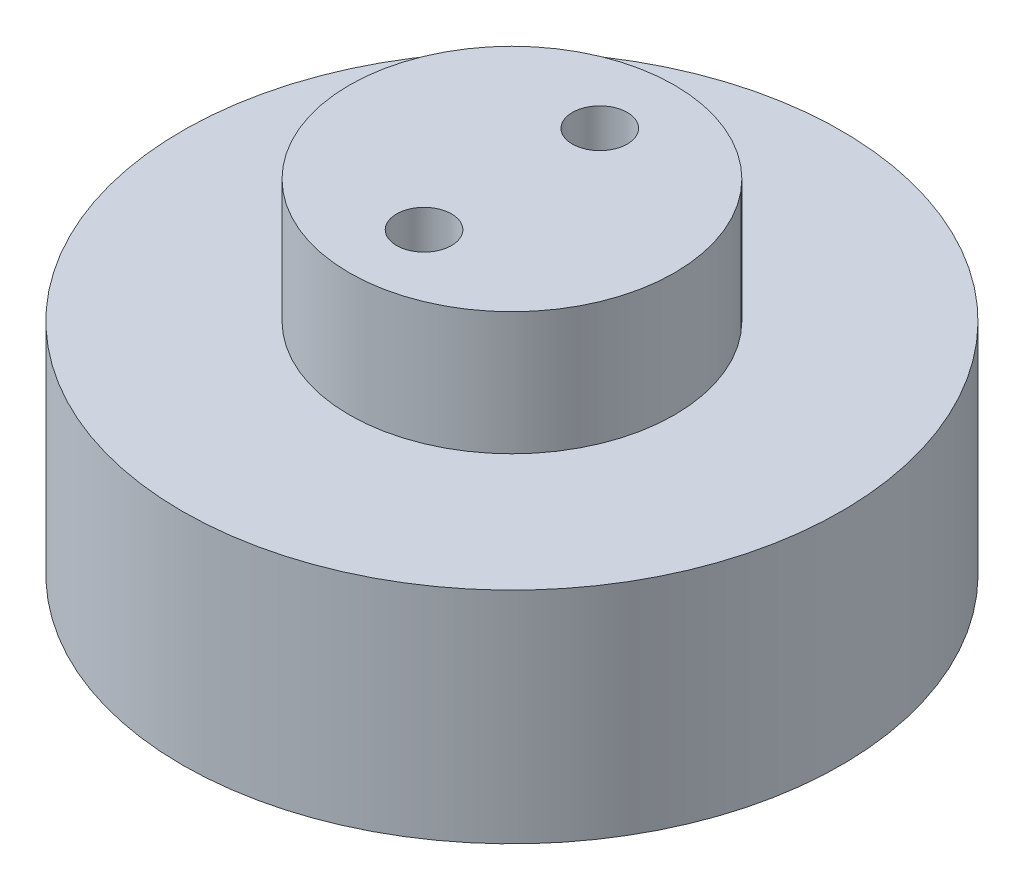
SolidWorks part; units mm, degrees
ref_plane "Front Plane" through (0, 0, 0) normal (0, 0, 1) x (1, 0, 0)
ref_plane "Top Plane" through (0, 0, 0) normal (0, 1, 0) x (1, 0, 0)
ref_plane "Right Plane" through (0, 0, 0) normal (1, 0, 0) x (0, 0, -1)
sketch "Sketch1" plane through (0, 0, 0) normal (0, 1, 0) x (1, 0, 0)
  circle A0 centre (0, 0) radius 19.05
  dimension "D1" = 38.1
extrude "Boss-Extrude1" add sketch "Sketch1" along normal blind 12.7
sketch "Sketch2" plane through (0, 12.7, 0) normal (0, 1, 0) x (1, 0, 0)
  circle A0 centre (0, 0) radius 9.398
  dimension "D1" = 18.796
extrude "Boss-Extrude2" add sketch "Sketch2" along normal blind 7.112
sketch "Sketch3" plane through (0, 0, 0) normal (0, -1, 0) x (1, 0, 0)
  circle A0 centre (0, 0) radius 2.921
  dimension "D1" = 5.842
extrude "Cut-Extrude1" [suppressed] cut sketch "Sketch3" against normal blind 17.272
sketch "Sketch4" [suppressed] plane through (0, 17.272, 0) normal (0, -1, 0) x (-1, 0, 0)
  circle A0 centre (0, 0) radius 1.5875
extrude "Cut-Extrude2" [suppressed] cut sketch "Sketch4" against normal blind 17.78
sketch "Sketch5" plane through (0, 0, 0) normal (0, -1, 0) x (1, 0, 0)
  line L1 (-5.394, 0) -> (-7.777, 4.1275)
  line L2 (-7.777, 4.1275) -> (-12.543, 4.1275)
  line L3 (-12.543, 4.1275) -> (-14.926, 0)
  line L4 (-14.926, 0) -> (-12.543, -4.1275)
  line L5 (-12.543, -4.1275) -> (-7.777, -4.1275)
  line L6 (-7.777, -4.1275) -> (-5.394, 0)
  line L7 (14.926, 0) -> (12.543, 4.1275)
  line L8 (12.543, 4.1275) -> (7.777, 4.1275)
  line L9 (7.777, 4.1275) -> (5.394, 0)
  line L10 (5.394, 0) -> (7.777, -4.1275)
  line L11 (7.777, -4.1275) -> (12.543, -4.1275)
  line L12 (12.543, -4.1275) -> (14.926, 0)
  circle A0 centre (-10.16, 0) radius 4.1275 construction
  circle A1 centre (10.16, 0) radius 4.1275 construction
  dimension "D1" = 8.255
  dimension "D2" = 8.255
  dimension "D3" = 10.16
  dimension "D4" = 20.32
extrude "Cut-Extrude3" cut sketch "Sketch5" against normal blind 3.175
sketch "Sketch6" plane through (0, 0, 0) normal (0, -1, 0) x (1, 0, 0)
  circle A0 centre (-10.16, 0) radius 1.5875
  circle A1 centre (10.16, 0) radius 1.5875
  dimension "D2" = 3.175
  dimension "D3" = 20.32
  dimension "D4" = 10.16
extrude "Cut-Extrude4" cut sketch "Sketch6" against normal blind 7.62
sketch "Sketch7" plane through (0, 0, 0) normal (0, -1, 0) x (1, 0, 0)
  circle A0 centre (0, 5.08) radius 2.921
  circle A1 centre (0, -5.08) radius 2.921
  dimension "D1" = 5.842
  dimension "D2" = 5.842
  dimension "D3" = 5.08
  dimension "D4" = 10.16
extrude "Cut-Extrude5" cut sketch "Sketch7" against normal blind 17.272
sketch "Sketch8" plane through (0, 17.272, 0) normal (0, -1, 0) x (1, 0, 0)
  circle A0 centre (0, 5.08) radius 1.5875
  circle A1 centre (0, -5.08) radius 1.5875
  dimension "D1" = 3.175
  dimension "D2" = 3.175
extrude "Cut-Extrude6" cut sketch "Sketch8" against normal through all
